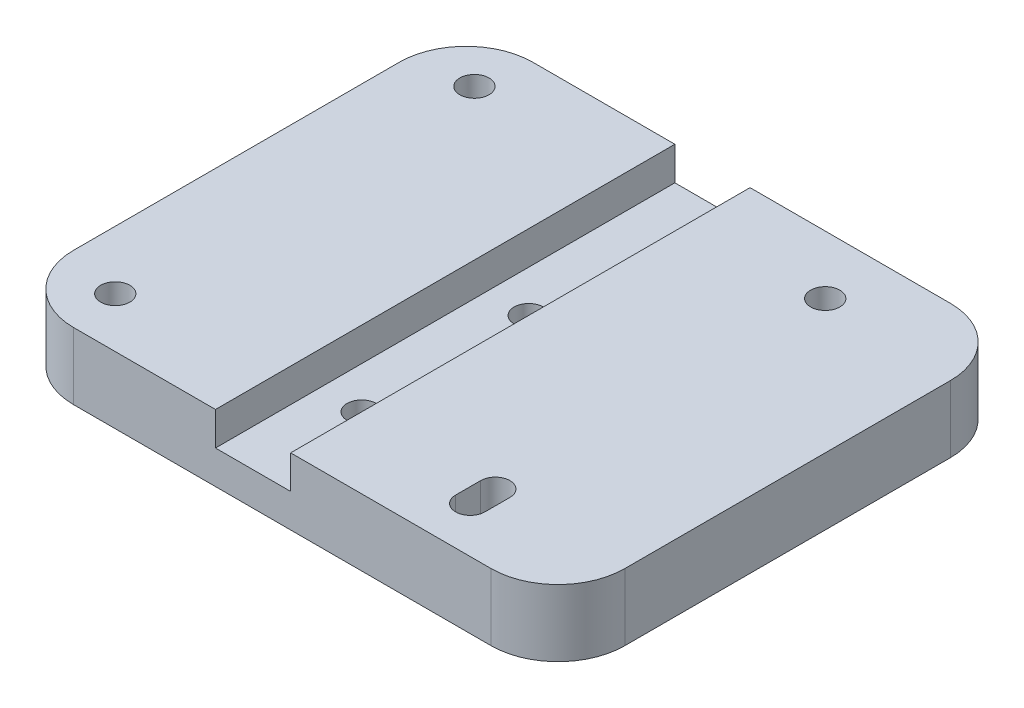
SolidWorks part; units mm, degrees
ref_plane "Plano frontal" through (0, 0, 0) normal (0, 0, 1) x (1, 0, 0)
ref_plane "Plano superior" through (0, 0, 0) normal (0, 1, 0) x (1, 0, 0)
ref_plane "Plano direito" through (0, 0, 0) normal (1, 0, 0) x (0, 0, -1)
sketch "Esboço1" plane through (0, 0, 0) normal (0, 0, 1) x (1, 0, 0)
  line L0 (0, 0) -> (75, 0)
  line L1 (75, 0) -> (75, 4)
  line L2 (75, 4) -> (0, 4)
  line L3 (0, 0) -> (0, 4)
  dimension "D1" = 4
  dimension "D3" = 75
extrude "Ressalto-extrusão1" add sketch "Esboço1" along normal blind 55
sketch "Esboço4" plane through (0, 0, 0) normal (0, -1, 0) x (1, 0, 0)
  line L0 (0, 55) -> (0, 0) construction
  line L1 (75, 55) -> (0, 55) construction
  line L2 (50, 48) -> (50, 7) construction
  line L3 (50, 49.5) -> (50, 46.5) construction
  line L4 (51.75, 49.5) -> (51.75, 46.5)
  line L5 (48.25, 49.5) -> (48.25, 46.5)
  line L6 (0, 55) -> (0, 0) construction
  line L7 (75, 55) -> (75, 0) construction
  line L8 (0, 27.5) -> (100, 27.5) construction
  arc A1 (51.75, 49.5) -> (48.25, 49.5) centre (50, 49.5) ccw
  circle A2 centre (50, 7) radius 1.75
  arc A3 (48.25, 46.5) -> (51.75, 46.5) centre (50, 46.5) ccw
  circle A6 centre (30, 22.5) radius 1.75
  circle A7 centre (30, 42.5) radius 1.75
  circle A8 centre (7, 49) radius 1.75
  circle A9 centre (7, 6) radius 1.75
  point P1 (50, 27.5)
  point P7 (0, 27.5)
  point P14 (50, 48)
  point P20 (19.002, 35.9856)
  point P31 (7, 49)
  point P32 (30, 22.5)
  dimension "D7" = 20
  dimension "D9" = 3.5
  dimension "D2" = 41
  dimension "D3" = 3
  dimension "D4" = 7
  dimension "D5" = 25
  dimension "D6" = 30
  dimension "D8" = 12.5
  dimension "D10" = 43
extrude "Corte-extrusão2" cut sketch "Esboço4" against normal through all
sketch "Esboço5" plane through (0, 4, 0) normal (0, 1, 0) x (1, 0, 0)
  line L0 (75, -55) -> (0, -55) construction
  line L1 (66, -55) -> (34, -55)
  line L2 (66, -55) -> (66, 0)
  line L3 (66, 0) -> (34, 0)
  line L4 (34, -55) -> (34, 0)
  line L5 (75, 0) -> (0, 0) construction
  line L6 (50, -7) -> (50, -46.5) construction
  line L7 (25, -55) -> (0, -55)
  line L8 (25, -55) -> (25, 0)
  line L9 (25, 0) -> (0, 0)
  line L10 (0, -55) -> (0, 0)
  line L11 (48.25, -49.5) -> (48.25, -46.5) construction
  line L12 (51.75, -46.5) -> (51.75, -49.5) construction
  line L13 (48.25, -49.5) -> (48.25, -46.5)
  line L14 (51.75, -46.5) -> (51.75, -49.5)
  circle A1 centre (50, -7) radius 1.75 construction
  arc A2 (51.75, -46.5) -> (48.25, -46.5) centre (50, -46.5) ccw construction
  circle A3 centre (7, -49) radius 1.75 construction
  circle A4 centre (7, -6) radius 1.75 construction
  arc A5 (48.25, -49.5) -> (51.75, -49.5) centre (50, -49.5) ccw construction
  circle A6 centre (7, -49) radius 1.75
  circle A7 centre (7, -6) radius 1.75
  circle A8 centre (50, -7) radius 1.75
  arc A9 (51.75, -46.5) -> (48.25, -46.5) centre (50, -46.5) ccw
  arc A10 (48.25, -49.5) -> (51.75, -49.5) centre (50, -49.5) ccw
  point P14 (50, 0)
  dimension "D1" = 32
  dimension "D2" = 25
extrude "Ressalto-extrusão2" add sketch "Esboço5" along normal blind 4
sketch "Esboço6" plane through (0, 0, 0) normal (0, -1, 0) x (1, 0, 0)
  line L0 (50, 46.5) -> (50, 49.5) construction
  line L1 (46, 46.5) -> (46, 49.5)
  line L2 (54, 46.5) -> (54, 49.5)
  circle A0 centre (50, 7) radius 4
  circle A1 centre (7, 6) radius 4
  circle A2 centre (7, 49) radius 4
  arc A3 (46, 46.5) -> (54, 46.5) centre (50, 46.5) ccw
  arc A4 (54, 49.5) -> (46, 49.5) centre (50, 49.5) ccw
  point P13 (50, 48)
  dimension "D1" = 4
extrude "Corte-extrusão3" cut sketch "Esboço6" against normal blind 4
sketch "Esboço7" plane through (0, 4, 0) normal (0, 1, 0) x (1, 0, 0)
  line L4 (75, -55) -> (75, 0)
  line L5 (75, 0) -> (66, 0)
  line L6 (66, 0) -> (66, -55)
  line L7 (66, -55) -> (75, -55)
  line L8 (75, -55) -> (75, 0)
  line L9 (75, 0) -> (66, 0)
  line L10 (66, 0) -> (66, -55)
  line L11 (66, -55) -> (75, -55)
  dimension "D1" = 0
extrude "Corte-extrusão4" cut sketch "Esboço7" against normal blind 10
fillet "Filete1" radius 8 4 edges at (0, 4, 0) (0, 4, 55) (66, 4, 0) (66, 4, 55)
